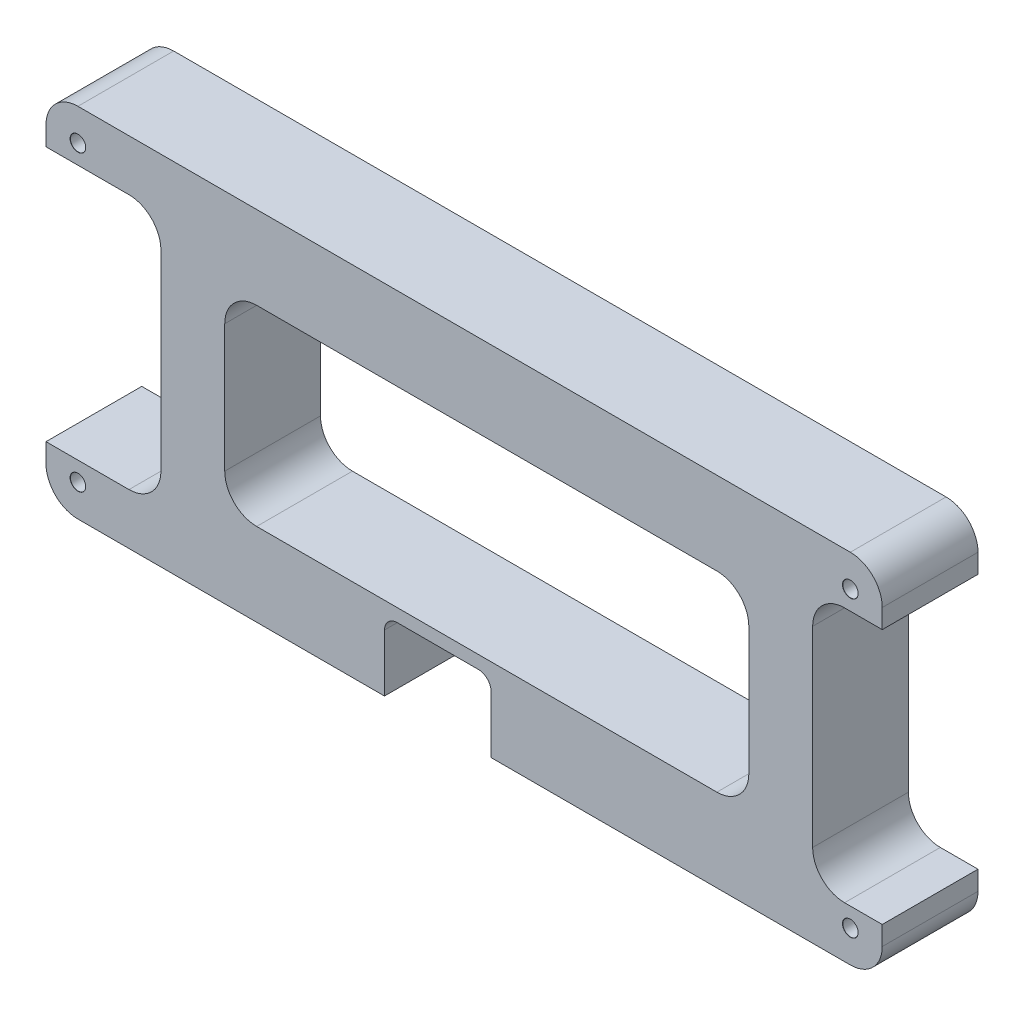
SolidWorks part; units mm, degrees
ref_plane "Спереди" through (0, 0, 0) normal (0, 0, 1) x (1, 0, 0)
ref_plane "Сверху" through (0, 0, 0) normal (0, 1, 0) x (1, 0, 0)
ref_plane "Справа" through (0, 0, 0) normal (1, 0, 0) x (0, 0, -1)
sketch "Эскиз8" plane through (0, 0, 0) normal (0, 0, 1) x (1, 0, 0)
  line L0 (126, 0) -> (126, 46) construction
  line L1 (-5, 0) -> (-5, 46) construction
  line L2 (0, 51) -> (121, 51) construction
  line L3 (0, -5) -> (121, -5) construction
  line L4 (50.025, -1.1376) -> (50.025, 3.9624)
  line L5 (50.025, 3.9624) -> (62.725, 3.9624)
  line L6 (62.725, -1.1376) -> (62.725, 3.9624)
  line L8 (50.025, -1.1376) -> (62.725, -1.1376)
  line L10 (49.875, -1.2776) -> (49.875, 4.1024)
  line L11 (49.875, 4.1024) -> (62.875, 4.1024)
  line L12 (62.875, -1.2776) -> (62.875, 4.1024)
  line L13 (49.875, -1.2776) -> (62.875, -1.2776)
  line L14 (56.025, 1.4124) -> (56.725, 1.4124)
  line L15 (56.375, 1.0624) -> (56.375, 1.7624)
  line L16 (50.495, 0.5424) -> (50.495, -0.2576)
  line L17 (50.895, -0.6576) -> (51.695, -0.6576)
  line L18 (52.095, -0.2576) -> (52.095, 0.5424)
  line L19 (51.695, 0.9424) -> (50.895, 0.9424)
  line L20 (50.025, 0.2073) -> (50.025, -1.1376)
  line L21 (50.025, -1.1376) -> (51.3699, -1.1376)
  line L22 (51.3699, -1.1376) -> (50.025, 0.2073)
  line L28 (120.0978, 38.2124) -> (135.1978, 38.2124) construction
  line L29 (120.0978, 23.4124) -> (120.0978, 38.2124) construction
  line L30 (120.0978, 23.4124) -> (135.1978, 23.4124) construction
  line L31 (135.1978, 23.4124) -> (135.1978, 38.2124) construction
  line L64 (120.0978, 20.6124) -> (135.1978, 20.6124) construction
  line L65 (120.0978, 5.8124) -> (120.0978, 20.6124) construction
  line L66 (120.0978, 5.8124) -> (135.1978, 5.8124) construction
  line L67 (135.1978, 5.8124) -> (135.1978, 20.6124) construction
  line L82 (-6.875, 27.6124) -> (8.975, 27.6124) construction
  line L83 (-6.875, 37.6124) -> (8.975, 37.6124) construction
  line L84 (8.975, 27.6124) -> (8.975, 37.6124) construction
  line L85 (-6.875, 27.6124) -> (-6.875, 37.6124) construction
  arc A0 (-5, 0) -> (0, -5) centre (0, 0) ccw construction
  arc A1 (0, 51) -> (-5, 46) centre (0, 46) ccw construction
  arc A2 (126, 46) -> (121, 51) centre (121, 46) ccw construction
  arc A3 (121, -5) -> (126, 0) centre (121, 0) ccw construction
  circle A4 centre (0, 0) radius 1.2 construction
  circle A5 centre (121, 0) radius 1.2 construction
  circle A6 centre (121, 46) radius 1.2 construction
  circle A7 centre (0, 46) radius 1.2 construction
  circle A8 centre (56.375, 1.4124) radius 0.25
  arc A9 (50.895, 0.9424) -> (50.495, 0.5424) centre (50.895, 0.5424) ccw
  arc A10 (50.495, -0.2576) -> (50.895, -0.6576) centre (50.895, -0.2576) ccw
  arc A11 (51.695, -0.6576) -> (52.095, -0.2576) centre (51.695, -0.2576) ccw
  arc A12 (52.095, 0.5424) -> (51.695, 0.9424) centre (51.695, 0.5424) ccw
  circle A13 centre (51.295, 0.1424) radius 0.5
  circle A14 centre (53.835, 0.1424) radius 0.8
  circle A15 centre (53.835, 0.1424) radius 0.5
  circle A16 centre (56.375, 0.1424) radius 0.8
  circle A17 centre (56.375, 0.1424) radius 0.5
  circle A18 centre (58.915, 0.1424) radius 0.8
  circle A19 centre (58.915, 0.1424) radius 0.5
  circle A20 centre (61.455, 0.1424) radius 0.8
  circle A21 centre (61.455, 0.1424) radius 0.5
  circle A22 centre (51.295, 2.6824) radius 0.8
  circle A23 centre (51.295, 2.6824) radius 0.5
  circle A24 centre (53.835, 2.6824) radius 0.8
  circle A25 centre (53.835, 2.6824) radius 0.5
  circle A26 centre (56.375, 2.6824) radius 0.8
  circle A27 centre (56.375, 2.6824) radius 0.5
  circle A28 centre (58.915, 2.6824) radius 0.8
  circle A29 centre (58.915, 2.6824) radius 0.5
  circle A30 centre (61.455, 2.6824) radius 0.8
  circle A31 centre (61.455, 2.6824) radius 0.5
  dimension "D1" = 131
  dimension "D2" = 56
sketch "Эскиз9" plane through (0, 0, 0) normal (0, 0, 1) x (1, 0, 0)
  line L4 (-5, 0) -> (-5, 46) construction
  line L7 (0, -5) -> (48.025, -5)
  line L9 (0, -5) -> (121, -5) construction
  line L10 (120.0978, 23.4124) -> (120.0978, 38.2124) construction
  line L12 (115.0978, 38) -> (115.0978, 8)
  line L13 (121, 51) -> (0, 51)
  line L14 (126, 46) -> (126, 43)
  line L15 (126, 43) -> (120.0978, 43)
  line L16 (-5, 46) -> (-5, 43)
  line L18 (126, 0) -> (126, 46) construction
  line L21 (-5, 0) -> (-5, 3)
  line L23 (126, 0) -> (126, 3)
  line L26 (120.0978, 3) -> (126, 3)
  line L32 (50.025, 3.9624) -> (62.725, 3.9624) construction
  line L34 (-5, 43) -> (8, 43)
  line L36 (-5, 3) -> (8, 3)
  line L37 (13, 38) -> (13, 8)
  line L43 (48.025, -5) -> (48.025, 3.9624)
  line L44 (50.025, 5.9624) -> (62.725, 5.9624)
  line L45 (64.725, -5) -> (64.725, 3.9624)
  line L54 (62.725, -1.1376) -> (62.725, 3.9624) construction
  line L55 (64.725, -5) -> (121, -5)
  line L57 (28, 38) -> (100.0978, 38)
  line L58 (23, 33) -> (23, 13)
  line L59 (28, 8) -> (100.0978, 8)
  line L60 (105.0978, 33) -> (105.0978, 13)
  arc A4 (120.0978, 43) -> (115.0978, 38) centre (120.0978, 38) ccw
  arc A5 (115.0978, 8) -> (120.0978, 3) centre (120.0978, 8) ccw
  arc A6 (121, -5) -> (126, 0) centre (121, 0) ccw
  arc A7 (-5, 0) -> (0, -5) centre (0, 0) ccw
  arc A8 (-5, 46) -> (0, 51) centre (0, 46) cw
  arc A9 (121, 51) -> (126, 46) centre (121, 46) cw
  arc A14 (8, 3) -> (13, 8) centre (8, 8) ccw
  arc A15 (8, 43) -> (13, 38) centre (8, 38) cw
  arc A16 (100.0978, 38) -> (105.0978, 33) centre (100.0978, 33) cw
  arc A17 (100.0978, 8) -> (105.0978, 13) centre (100.0978, 13) ccw
  arc A18 (23, 13) -> (28, 8) centre (28, 13) ccw
  arc A19 (28, 38) -> (23, 33) centre (28, 33) ccw
  arc A20 (62.725, 5.9624) -> (64.725, 3.9624) centre (62.725, 3.9624) cw
  arc A21 (48.025, 3.9624) -> (50.025, 5.9624) centre (50.025, 3.9624) cw
  point P32 (-5, 44.5)
  point P43 (126, -5)
  point P46 (-5, -5)
  point P51 (60.0489, 3)
  point P53 (56.375, 3.9624)
  dimension "D10" = 5
  dimension "D15" = 5
  dimension "D16" = 2
  dimension "D1" = 8
  dimension "D2" = 8
  dimension "D4" = 5
  dimension "D7" = 56
  dimension "D9" = 8
  dimension "D3" = 8
  dimension "D8" = 18
  dimension "D5" = 2
  dimension "D6" = 2
  dimension "D11" = 2
  dimension "D12" = 10
  dimension "D13" = 10
  dimension "D14" = 131
extrude "Бобышка-Вытянуть1" add sketch "Эскиз9" against normal blind 15
hole_wizard "Отверстие с зазором M21" positions "Эскиз10" profile "Эскиз11" hole size "M2" standard "ISO" end condition through all
sketch "Эскиз10" plane through (0, 0, 0) normal (0, 0, 1) x (1, 0, 0)
  point P0 (0, 46)
  point P3 (0, 0)
  point P6 (121, 0)
  point P9 (121, 46)
sketch "Эскиз11" plane through (0, 46, 0) normal (1, 0, 0) x (0, -1, 0)
  line L0 (0, 0) -> (0, 15)
  line L1 (0, 15) -> (1.2, 15)
  line L2 (1.2, 15) -> (1.2, 0.025)
  line L3 (1.2, 0.025) -> (1.225, 0)
  line L5 (1.225, 0) -> (0, 0)
  line L6 (-1.2, 0.025) -> (-1.225, 0) construction
  line L11 (0, -6.35) -> (0, 107.95) construction
  dimension "Диаметр сквозного отверстия" = 2.4
  dimension "Глубина сквозного отверстия" = 15
  dimension "Диаметр передней зенковки" = 2.45
  dimension "Угол передней зенковки" = 90
hole_wizard "Отверстия под штифты Ø5.0 мм1" positions "Эскиз14" profile "Эскиз15" hole size "Ø5.0" standard "ISO"
sketch "Эскиз14" plane through (0, 0, -15) normal (0, 0, -1) x (-1, 0, 0)
  point P0 (-121, 0)
  point P3 (-121, 46)
  point P6 (0, 46)
  point P9 (0, 0)
  point P14 (-55.1166, 0)
sketch "Эскиз15" plane through (121, 0, -15) normal (1, 0, 0) x (0, 1, 0)
  line L0 (0, 0) -> (0, 5)
  line L1 (0, 5) -> (2.5, 3.4978)
  line L2 (2.5, 3.4978) -> (2.5, 0.025)
  line L3 (2.5, 0.025) -> (2.525, 0)
  line L5 (2.525, 0) -> (0, 0)
  line L6 (-2.5, 0.025) -> (-2.525, 0) construction
  line L10 (0, 5) -> (-2.5, 3.4978) construction
  line L11 (0, -6.35) -> (0, 107.95) construction
  dimension "Диаметр отверстия" = 5
  dimension "Глубина отверстия" = 5
  dimension "Диаметр передней зенковки" = 5.05
  dimension "Угол передней зенковки" = 90
  dimension "Угол заточки сверла" = 118
ref_plane "Плоскость1" through (0, 0, -35) normal (0, 0, -1) x (-1, 0, 0)
sketch "Эскиз16" plane through (0, 0, -15) normal (0, 0, -1) x (-1, 0, 0)
  circle A0 centre (-121, 46) radius 2.5
  circle A2 centre (0, 0) radius 2.5
  circle A3 centre (-121, 0) radius 2.5
  circle A5 centre (0, 46) radius 2.5
  dimension "D1" = 5
equation "\"D9@Эскиз9\"=\"D3@Эскиз9\""
